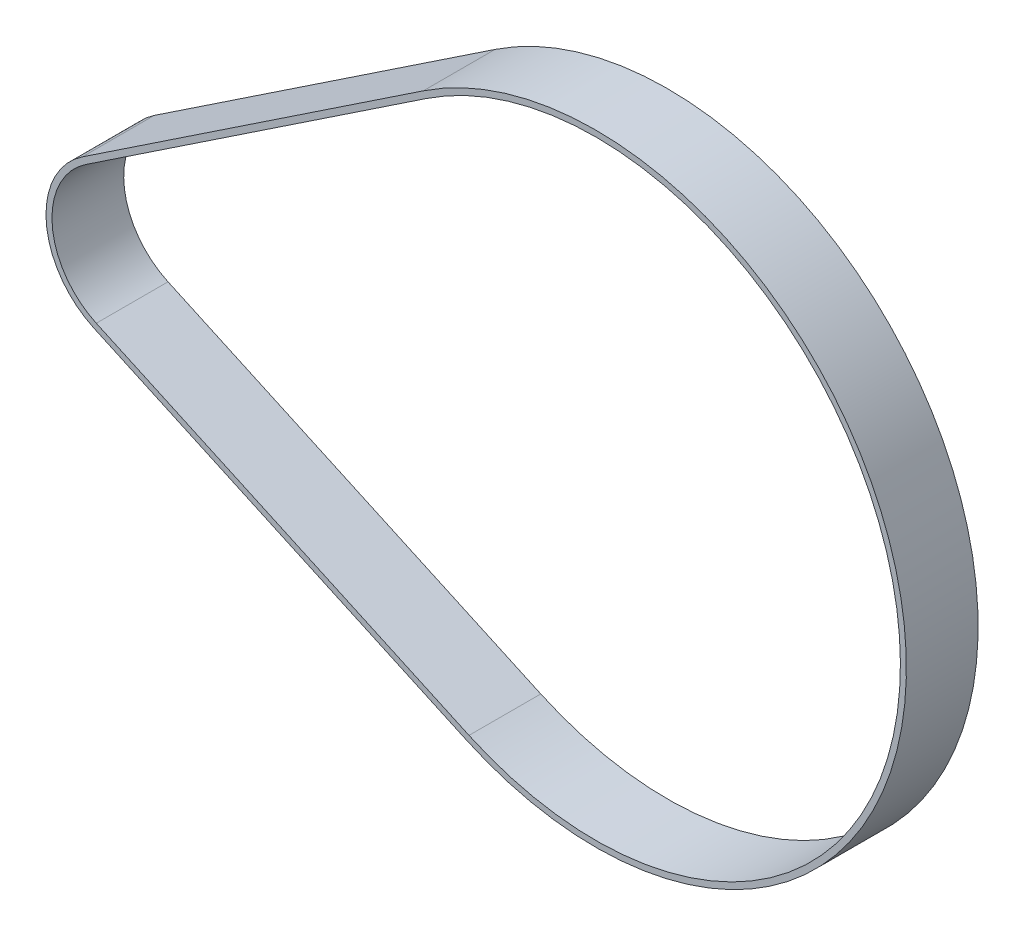
SolidWorks part; units mm, degrees
ref_plane "Front Plane" through (0, 0, 0) normal (0, 0, 1) x (1, 0, 0)
ref_plane "Top Plane" through (0, 0, 0) normal (0, 1, 0) x (1, 0, 0)
ref_plane "Right Plane" through (0, 0, 0) normal (1, 0, 0) x (0, 0, -1)
sketch "Sketch2" plane through (0, 0, 0) normal (0, 0, 1) x (1, 0, 0)
  line L0 (0, 0) -> (1, 0) construction
  line L1 (0, 0) -> (0, 1) construction
  line L2 (-3.5262, 5.281) -> (24.9859, 24.319)
  line L3 (28.5323, -20.0405) -> (-2.6424, -5.7741)
  arc A0 (-2.6424, -5.7741) -> (-3.5262, 5.281) centre (0, 0) cw
  arc A1 (24.9859, 24.319) -> (28.5323, -20.0405) centre (39.1351, 3.1287) cw
sketch "Sketch3" plane through (0, 0, 0) normal (0, 0, 1) x (1, 0, 0)
  line L0 (-3.5262, 5.281) -> (24.9859, 24.319) construction
  line L1 (28.5323, -20.0405) -> (-2.6424, -5.7741) construction
  line L2 (-3.5262, 5.281) -> (24.9859, 24.319)
  line L3 (28.5323, -20.0405) -> (-2.6424, -5.7741)
  line L4 (-3.8038, 5.6968) -> (24.7083, 24.7349)
  line L5 (28.3243, -20.4951) -> (-2.8504, -6.2288)
  arc A0 (-3.5262, 5.281) -> (-2.6424, -5.7741) centre (0, 0) ccw construction
  arc A1 (28.5323, -20.0405) -> (24.9859, 24.319) centre (39.1351, 3.1287) ccw construction
  arc A2 (-3.5262, 5.281) -> (-2.6424, -5.7741) centre (0, 0) ccw
  arc A3 (28.5323, -20.0405) -> (24.9859, 24.319) centre (39.1351, 3.1287) ccw
  arc A4 (28.3243, -20.4951) -> (24.7083, 24.7349) centre (39.1351, 3.1287) ccw
  arc A5 (-3.8038, 5.6968) -> (-2.8504, -6.2288) centre (0, 0) ccw
  dimension "D1" = 0.5
extrude "Boss-Extrude1" add sketch "Sketch3" along normal blind 4 and the other way blind 2
